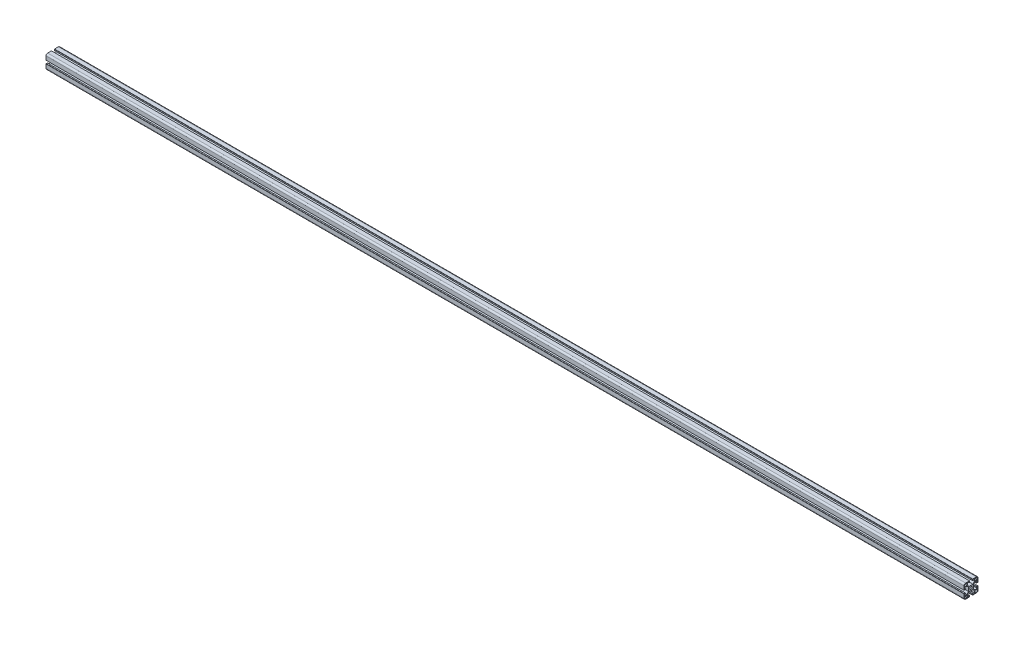
SolidWorks part; units mm, degrees
ref_plane "前视基准面" through (0, 0, 0) normal (0, 0, 1) x (1, 0, 0)
ref_plane "上视基准面" through (0, 0, 0) normal (0, 1, 0) x (1, 0, 0)
ref_plane "右视基准面" through (0, 0, 0) normal (1, 0, 0) x (0, 0, -1)
sketch "草图3" plane through (0, 0, 0) normal (1, 0, 0) x (0, 0, -1)
  line L1 (-15.5, -20) -> (-4.5, -20)
  line L2 (-20, -15.5) -> (-20, -4.5)
  line L3 (-15.5, 20) -> (-4.5, 20)
  line L4 (20, -15.5) -> (20, -4.5)
  line L8 (-20, 4.5) -> (-19.5, 4.5)
  line L9 (-19.5, 4.5) -> (-19.5, 4.1)
  line L10 (-19.5, 4.1) -> (-16.2, 4.1)
  line L11 (-16.2, 4.1) -> (-16.2, 6.4)
  line L12 (-16.2, 6.4) -> (-18.2, 6.4)
  line L13 (-18.2, 6.4) -> (-18.2, 10.25)
  line L14 (-18.2, 10.25) -> (-11.5228, 10.25)
  line L15 (-11.5228, 10.25) -> (-6.7519, 5.4791)
  line L16 (-6.7519, 5.4791) -> (-6.7519, -5.4791)
  line L21 (6.7519, 5.4791) -> (6.7519, -5.4791)
  line L22 (11.5228, 10.25) -> (6.7519, 5.4791)
  line L23 (18.2, 10.25) -> (11.5228, 10.25)
  line L24 (18.2, 6.4) -> (18.2, 10.25)
  line L25 (16.2, 6.4) -> (18.2, 6.4)
  line L26 (16.2, 4.1) -> (16.2, 6.4)
  line L27 (19.5, 4.1) -> (16.2, 4.1)
  line L28 (19.5, 4.5) -> (19.5, 4.1)
  line L29 (20, 4.5) -> (19.5, 4.5)
  line L30 (20, -4.5) -> (19.5, -4.5)
  line L31 (19.5, -4.5) -> (19.5, -4.1)
  line L32 (19.5, -4.1) -> (16.2, -4.1)
  line L33 (16.2, -4.1) -> (16.2, -6.4)
  line L34 (16.2, -6.4) -> (18.2, -6.4)
  line L35 (18.2, -6.4) -> (18.2, -10.25)
  line L36 (18.2, -10.25) -> (11.5228, -10.25)
  line L37 (11.5228, -10.25) -> (6.7519, -5.4791)
  line L38 (-11.5228, -10.25) -> (-6.7519, -5.4791)
  line L39 (-18.2, -10.25) -> (-11.5228, -10.25)
  line L40 (-18.2, -6.4) -> (-18.2, -10.25)
  line L41 (-16.2, -6.4) -> (-18.2, -6.4)
  line L42 (-16.2, -4.1) -> (-16.2, -6.4)
  line L43 (-19.5, -4.1) -> (-16.2, -4.1)
  line L44 (-19.5, -4.5) -> (-19.5, -4.1)
  line L45 (-20, -4.5) -> (-19.5, -4.5)
  line L46 (-4.5, -20) -> (-4.5, -19.5)
  line L47 (-4.5, -19.5) -> (-4.1, -19.5)
  line L48 (-4.1, -19.5) -> (-4.1, -16.2)
  line L49 (-4.1, -16.2) -> (-6.4, -16.2)
  line L50 (-6.4, -16.2) -> (-6.4, -18.2)
  line L51 (-6.4, -18.2) -> (-10.25, -18.2)
  line L52 (-10.25, -18.2) -> (-10.25, -11.5228)
  line L53 (-10.25, -11.5228) -> (-5.4791, -6.7519)
  line L56 (5.4791, -6.7519) -> (-5.4791, -6.7519)
  line L57 (10.25, -11.5228) -> (5.4791, -6.7519)
  line L58 (10.25, -18.2) -> (10.25, -11.5228)
  line L59 (6.4, -18.2) -> (10.25, -18.2)
  line L60 (6.4, -16.2) -> (6.4, -18.2)
  line L61 (4.1, -16.2) -> (6.4, -16.2)
  line L62 (4.1, -19.5) -> (4.1, -16.2)
  line L63 (4.5, -19.5) -> (4.1, -19.5)
  line L64 (4.5, -20) -> (4.5, -19.5)
  line L65 (-10.25, 11.5228) -> (-5.4791, 6.7519)
  line L66 (-10.25, 18.2) -> (-10.25, 11.5228)
  line L67 (-6.4, 18.2) -> (-10.25, 18.2)
  line L68 (-6.4, 16.2) -> (-6.4, 18.2)
  line L69 (-4.1, 16.2) -> (-6.4, 16.2)
  line L70 (-4.1, 19.5) -> (-4.1, 16.2)
  line L71 (-4.5, 19.5) -> (-4.1, 19.5)
  line L72 (-4.5, 20) -> (-4.5, 19.5)
  line L73 (4.5, 20) -> (4.5, 19.5)
  line L74 (4.5, 19.5) -> (4.1, 19.5)
  line L75 (4.1, 19.5) -> (4.1, 16.2)
  line L76 (4.1, 16.2) -> (6.4, 16.2)
  line L77 (6.4, 16.2) -> (6.4, 18.2)
  line L78 (6.4, 18.2) -> (10.25, 18.2)
  line L79 (10.25, 18.2) -> (10.25, 11.5228)
  line L80 (10.25, 11.5228) -> (5.4791, 6.7519)
  line L81 (5.4791, 6.7519) -> (-5.4791, 6.7519)
  line L82 (20, 4.5) -> (20, 15.5)
  line L84 (4.5, 20) -> (15.5, 20)
  line L85 (-20, 4.5) -> (-20, 15.5)
  line L86 (4.5, -20) -> (15.5, -20)
  arc A0 (-15.5, -20) -> (-20, -15.5) centre (-15.5, -15.5) cw
  arc A1 (15.5, -20) -> (20, -15.5) centre (15.5, -15.5) ccw
  arc A2 (15.5, 20) -> (20, 15.5) centre (15.5, 15.5) cw
  arc A3 (-20, 15.5) -> (-15.5, 20) centre (-15.5, 15.5) cw
  circle A4 centre (0, 0) radius 3.4
  point P0 (0, 0)
  dimension "D3" = 4.5
  dimension "D4" = 6.8
  dimension "D7" = 1.8
  dimension "D10" = 0.5
  dimension "D11" = 13.2481
  dimension "D13" = 2
extrude "凸台-拉伸1" add sketch "草图3" along normal up to vertex (2622 mm away)
ref_plane "基准面1" through (2622, -20, 15.5) normal (-1, 0, 0) x (0, 0, 1)
sketch "草图4" plane through (2622, -20, 15.5) normal (-1, 0, 0) x (0, 0, 1)
  line L0 (-5.25, 31.5228) -> (-5.25, 38.2) construction
  line L1 (-3.75, 31.75) -> (3, 31.75)
  line L2 (-3.75, 31.75) -> (-3.75, 38.5)
  line L3 (-3.75, 38.5) -> (0, 38.5)
  line L4 (3, 31.75) -> (3, 35.5)
  line L5 (4.5, 35.5) -> (4.5, 24.5) construction
  line L6 (-11, 40) -> (0, 40) construction
  line L7 (2.7, 30.25) -> (-3.9772, 30.25) construction
  line L8 (-3.75, 8.25) -> (-3.75, 1.5)
  line L9 (-3.75, 8.25) -> (3, 8.25)
  line L10 (3, 8.25) -> (3, 4.5)
  line L11 (-3.75, 1.5) -> (0, 1.5)
  line L12 (-27.25, 8.25) -> (-34, 8.25)
  line L13 (-27.25, 8.25) -> (-27.25, 1.5)
  line L14 (-27.25, 1.5) -> (-31, 1.5)
  line L15 (-34, 8.25) -> (-34, 4.5)
  line L16 (-27.25, 31.75) -> (-27.25, 38.5)
  line L17 (-27.25, 31.75) -> (-34, 31.75)
  line L18 (-34, 31.75) -> (-34, 35.5)
  line L19 (-27.25, 38.5) -> (-31, 38.5)
  arc A0 (0, 38.5) -> (3, 35.5) centre (0, 35.5) cw
  arc A1 (3, 4.5) -> (0, 1.5) centre (0, 4.5) cw
  arc A2 (-31, 1.5) -> (-34, 4.5) centre (-31, 4.5) cw
  arc A3 (-34, 35.5) -> (-31, 38.5) centre (-31, 35.5) cw
  dimension "D5" = 3
  dimension "D1" = 1.5
  dimension "D2" = 1.5
  dimension "D3" = 1.5
  dimension "D4" = 1.5
  dimension "D6" = 4
extrude "切除-拉伸3" cut sketch "草图4" along normal blind 3297
